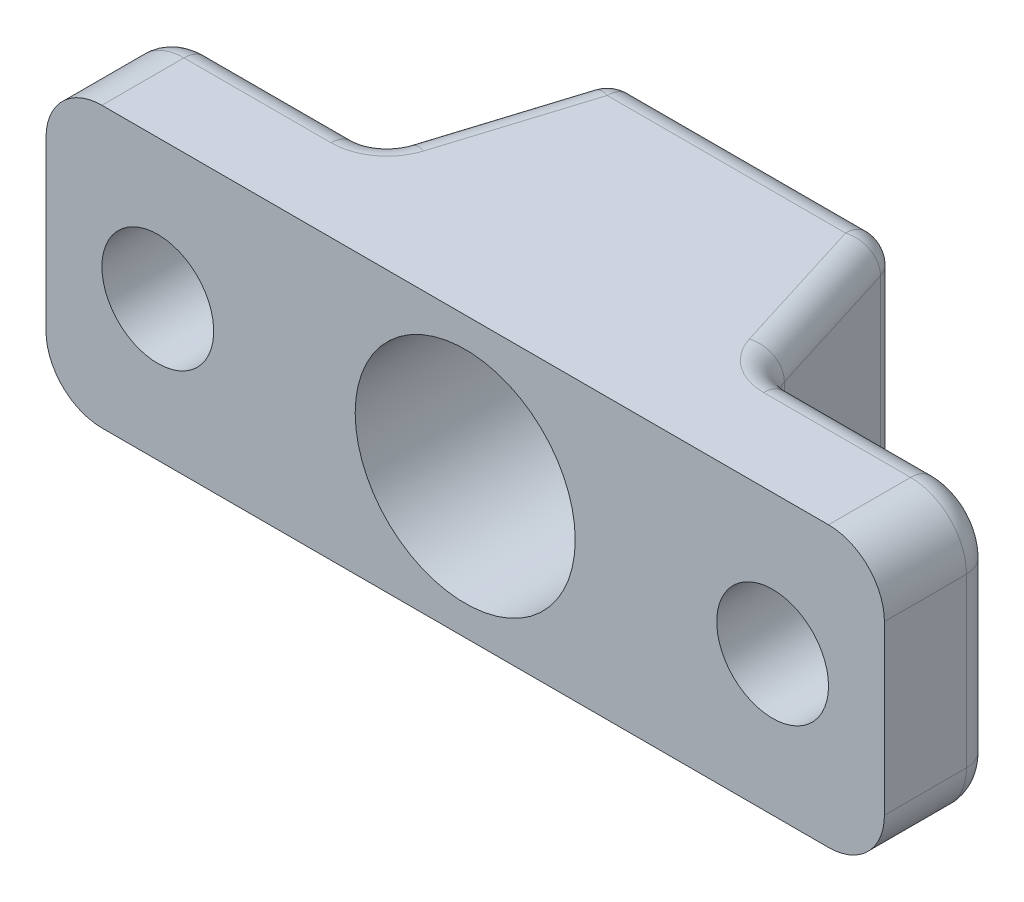
SolidWorks part; units mm, degrees
material "ABS"
ref_plane "Front Plane" through (0, 0, 0) normal (0, 0, 1) x (1, 0, 0)
ref_plane "Top Plane" through (0, 0, 0) normal (0, 1, 0) x (1, 0, 0)
ref_plane "Right Plane" through (0, 0, 0) normal (1, 0, 0) x (0, 0, -1)
sketch "Sketch1" plane through (0, 0, 0) normal (0, 1, 0) x (1, 0, 0)
  line L0 (19.05, 0) -> (-19.05, 0)
  line L1 (-19.05, 0) -> (-19.05, 5)
  line L2 (-19.05, 5) -> (-8.89, 5)
  line L3 (-8.89, 5) -> (-6.35, 13.1378)
  line L4 (-6.35, 13.1378) -> (6.35, 13.1378)
  line L5 (6.35, 13.1378) -> (8.89, 5)
  line L6 (8.89, 5) -> (19.05, 5)
  line L7 (19.05, 5) -> (19.05, 0)
  line L8 (0, 0) -> (0, 13.1378) construction
  line L9 (-5, 0) -> (-5, 13.1378) construction
  line L10 (5, 0) -> (5, 13.1378) construction
  point P0 (0, 13.1378)
  point P4 (0, 0)
  dimension "D1" = 5
  dimension "D2" = 38.1
  dimension "D3" = 12.7
  dimension "D6" = 10.16
  dimension "D4" = 5
  dimension "D5" = 5
extrude "Boss-Extrude1" add sketch "Sketch1" along normal blind 12.7
sketch "Sketch2" plane through (0, 0, -13.1378) normal (0, 0, -1) x (-1, 0, 0)
  line L0 (6.35, 12.7) -> (6.35, 0) construction
  circle A0 centre (0, 6.35) radius 5
  point P4 (6.35, 6.35)
  point P5 (0, 6.35)
  dimension "D1" = 10
extrude "Cut-Extrude1" cut sketch "Sketch2" against normal through all
sketch "Sketch3" plane through (0, 0, -5) normal (0, 0, -1) x (-1, 0, 0)
  line L0 (19.05, 12.7) -> (19.05, 0) construction
  line L1 (0, 0) -> (0, 4.5896) construction
  circle A0 centre (13.97, 6.35) radius 2.54
  circle A1 centre (-13.97, 6.35) radius 2.54
  point P5 (19.05, 6.35)
  dimension "D1" = 5.08
extrude "Cut-Extrude2" cut sketch "Sketch3" against normal through all
fillet "Fillet1" radius 2.54 4 edges at (-19.05, 0, -2.5) (19.05, 0, -2.5) (19.05, 12.7, -2.5) (-19.05, 12.7, -2.5)
fillet "Fillet2" radius 1.27 20 edges at (-18.3061, 11.9561, -5) (-19.05, 6.35, -5) (-18.3061, 0.7439, -5) (12.7, 12.7, -5) (18.3061, 11.9561, -5) (19.05, 6.35, -5) (18.3061, 0.7439, -5) (8.89, 6.35, -5) (7.62, 12.7, -9.0689) (6.35, 6.35, -13.1378) (7.62, 0, -9.0689) (-6.35, 6.35, -13.1378) (-7.62, 12.7, -9.0689) (-8.89, 6.35, -5) (-7.62, 0, -9.0689) (0, 12.7, -13.1378) (-12.7, 12.7, -5) (-12.7, 0, -5) (0, 0, -13.1378) (12.7, 0, -5)
